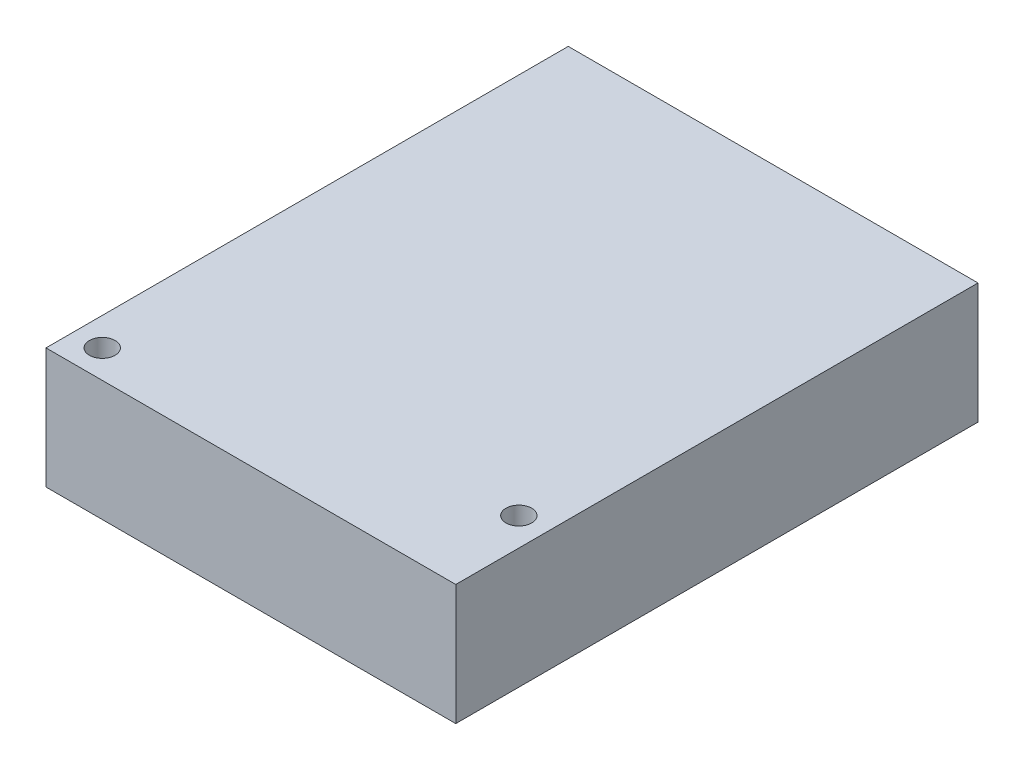
SolidWorks part; units mm, degrees
ref_plane "Front Plane" through (0, 0, 0) normal (0, 0, 1) x (1, 0, 0)
ref_plane "Top Plane" through (0, 0, 0) normal (0, 1, 0) x (1, 0, 0)
ref_plane "Right Plane" through (0, 0, 0) normal (1, 0, 0) x (0, 0, -1)
sketch "Sketch1" plane through (0, 0, 0) normal (0, 1, 0) x (1, 0, 0)
  line L1 (25.5, -32.5) -> (-25.5, -32.5)
  line L2 (25.5, -32.5) -> (25.5, 32.5)
  line L3 (25.5, 32.5) -> (-25.5, 32.5)
  line L4 (-25.5, -32.5) -> (-25.5, 32.5)
  line L5 (25.5, -32.5) -> (-25.5, 32.5) construction
  line L6 (25.5, 32.5) -> (-25.5, -32.5) construction
  circle A0 centre (-22, -29) radius 1.6
  circle A1 centre (22, -21.15) radius 1.6
  point P0 (0, 0)
  dimension "D3" = 3.2
  dimension "D6" = 3.2
  dimension "D1" = 65
  dimension "D2" = 51
  dimension "D4" = 3.5
  dimension "D5" = 3.5
  dimension "D7" = 11.35
  dimension "D8" = 3.5
extrude "Boss-Extrude1" add sketch "Sketch1" along normal blind 15
